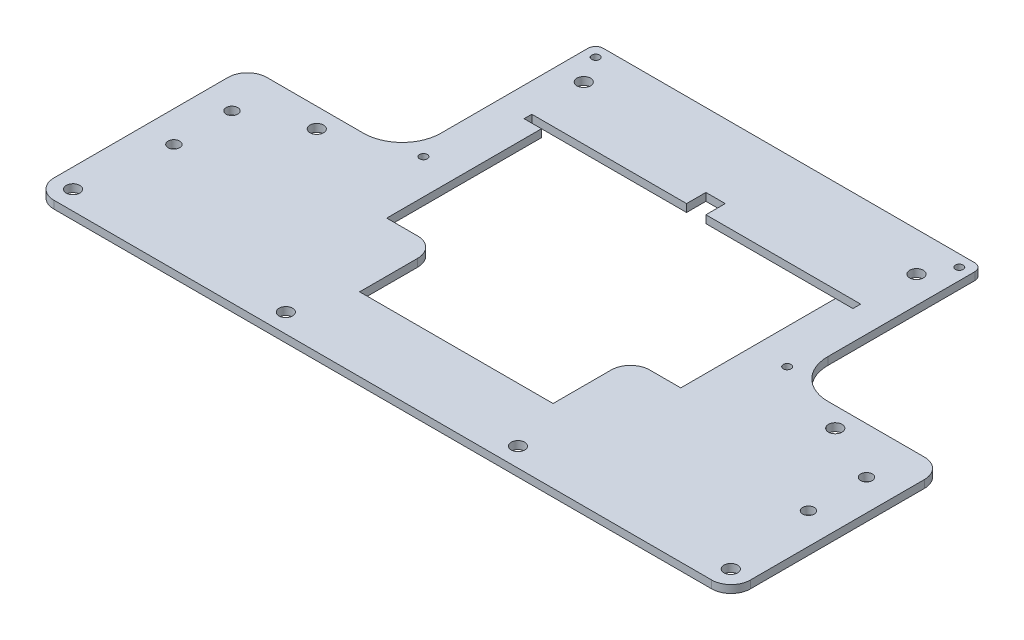
SolidWorks part; units mm, degrees
material "Acrylic (Medium-high impact)"
ref_plane "Front Plane" through (0, 0, 0) normal (0, 0, 1) x (1, 0, 0)
ref_plane "Top Plane" through (0, 0, 0) normal (0, 1, 0) x (1, 0, 0)
ref_plane "Right Plane" through (0, 0, 0) normal (1, 0, 0) x (0, 0, -1)
sketch "Sketch1" plane through (0, 0, 0) normal (0, 1, 0) x (1, 0, 0)
  line L0 (-85, -27.536) -> (-85, 17.464) construction
  line L2 (-90, 32.536) -> (-90, -32.464)
  line L3 (-90, -32.464) -> (90, -32.464)
  line L4 (90, 32.536) -> (90, -32.464)
  line L5 (-90, 32.536) -> (90, -32.464) construction
  line L6 (-90, -32.464) -> (90, 32.536) construction
  line L7 (-85, 17.464) -> (-67, 17.464) construction
  line L8 (-90, 32.536) -> (-50, 32.536)
  line L9 (0, -55) -> (0, 55) construction
  line L10 (-85, -27.536) -> (-30, -27.536) construction
  line L13 (-50, 32.536) -> (-50, 72.536)
  line L24 (-50, 72.536) -> (50, 72.536)
  line L25 (50, 72.536) -> (50, 32.536)
  line L26 (50, 32.536) -> (90, 32.536)
  line L27 (-50, 72.536) -> (-47, 72.536) construction
  line L28 (-47, 72.536) -> (-47, 69.536) construction
  line L29 (-47, 69.536) -> (-47, 25.036) construction
  circle A1 centre (-85, -27.536) radius 1.75
  circle A2 centre (85, -27.536) radius 1.75
  circle A13 centre (-30, -27.536) radius 1.75
  circle A17 centre (30, -27.536) radius 1.75
  circle A20 centre (-67, 17.464) radius 1.75
  circle A21 centre (67, 17.464) radius 1.75
  circle A22 centre (-47, 69.536) radius 1
  circle A23 centre (-47, 25.036) radius 1
  circle A24 centre (47, 25.036) radius 1
  circle A25 centre (47, 69.536) radius 1
  dimension "D5" = 3.5
  dimension "D9" = 3.5
  dimension "D15" = 40
  dimension "D16" = 40
  dimension "D20" = 2
  dimension "D22" = 2
  dimension "D1" = 65
  dimension "D2" = 180
  dimension "D3" = 45
  dimension "D4" = 18
  dimension "D6" = 55
  dimension "D17" = 100
  dimension "D18" = 3
  dimension "D19" = 3
  dimension "D21" = 44.5
extrude "Boss-Extrude1" add sketch "Sketch1" along normal blind 2
sketch "Sketch3" plane through (0, 2, 0) normal (0, 1, 0) x (1, 0, 0)
  line L0 (0, -32.464) -> (0, -7.464) construction
  line L1 (-90, -32.464) -> (90, -32.464) construction
  line L2 (0, -7.464) -> (0, 47.536) construction
  line L3 (2.5, 48.536) -> (42.5, 48.536)
  line L4 (-42.5, 48.536) -> (-2.5, 48.536)
  line L5 (-42.5, 48.536) -> (-42.5, 46.536)
  line L6 (-42.5, 46.536) -> (-38, 46.536)
  line L7 (42.5, 48.536) -> (42.5, 46.536)
  line L8 (-42.5, 48.536) -> (42.5, 46.536) construction
  line L9 (-42.5, 46.536) -> (42.5, 48.536) construction
  line L10 (38, 46.536) -> (42.5, 46.536)
  line L11 (-38, 6.536) -> (-25, 6.536)
  line L12 (-38, 6.536) -> (-38, 46.536)
  line L14 (38, 6.536) -> (38, 46.536)
  line L15 (-38, 6.536) -> (38, 46.536) construction
  line L16 (-38, 46.536) -> (38, 6.536) construction
  line L17 (-2.5, 53.536) -> (2.5, 53.536)
  line L18 (-2.5, 53.536) -> (-2.5, 48.536)
  line L20 (2.5, 53.536) -> (2.5, 48.536)
  line L21 (-25, 6.536) -> (-25, -13.464)
  line L22 (-25, -13.464) -> (25, -13.464)
  line L23 (25, -13.464) -> (25, 6.536)
  line L24 (25, 6.536) -> (38, 6.536)
  line L25 (-67, 17.464) -> (-43, 17.464) construction
  line L26 (90, 32.536) -> (50, 32.536)
  line L27 (90, 32.536) -> (90, 22.536)
  line L28 (90, 22.536) -> (50, 22.536)
  line L29 (50, 32.536) -> (50, 22.536)
  line L30 (-90, 32.536) -> (-50, 32.536)
  line L31 (-90, 32.536) -> (-90, 22.536)
  line L32 (-90, 22.536) -> (-50, 22.536)
  line L33 (-50, 32.536) -> (-50, 22.536)
  line L34 (-43, 17.464) -> (-43, 62.464) construction
  circle A3 centre (-43, 62.464) radius 1.75
  circle A4 centre (43, 62.464) radius 1.75
  point P10 (0, 48.536)
  dimension "D13" = 45
  dimension "D14" = 3.5
  dimension "D1" = 25
  dimension "D2" = 55
  dimension "D3" = 2
  dimension "D4" = 85
  dimension "D5" = 40
  dimension "D6" = 76
  dimension "D7" = 20
  dimension "D8" = 5
  dimension "D9" = 50
  dimension "D10" = 10
  dimension "D11" = 10
  dimension "D12" = 24
extrude "Cut-Extrude2" cut sketch "Sketch3" against normal blind 10
fillet "Fillet1" radius 2 2 edges at (50, 1, -72.536) (-50, 1, -72.536)
fillet "Fillet2" radius 5 6 edges at (-90, 1, 32.464) (-90, 1, -22.536) (25, 1, -6.536) (-25, 1, -6.536) (90, 1, 32.464) (90, 1, -22.536)
fillet "Fillet3" radius 10 2 edges at (50, 1, -22.536) (-50, 1, -22.536)
sketch "Sketch4" plane through (0, 2, 0) normal (0, 1, 0) x (1, 0, 0)
  line L0 (-90, 17.536) -> (-82, 17.536) construction
  line L1 (-82, 17.536) -> (-82, 10.536) construction
  line L2 (-82, 10.536) -> (-82, -4.464) construction
  line L3 (0, -1.1) -> (0, 1.1) construction
  circle A0 centre (-82, 10.536) radius 1.5
  circle A1 centre (-82, -4.464) radius 1.5
  circle A2 centre (82, 10.536) radius 1.5
  circle A3 centre (82, -4.464) radius 1.5
  dimension "D4" = 3
  dimension "D5" = 3
  dimension "D1" = 8
  dimension "D2" = 7
  dimension "D3" = 15
extrude "Cut-Extrude3" cut sketch "Sketch4" against normal blind 10
